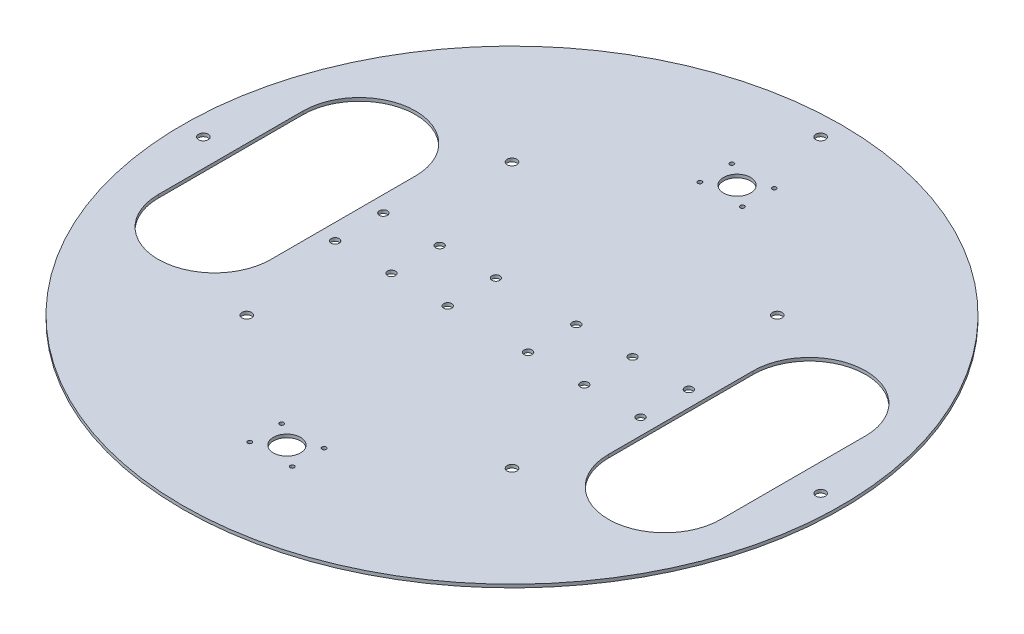
SolidWorks part; units mm, degrees
material "5052-H34"
ref_plane "Front Plane" through (0, 0, 0) normal (0, 0, 1) x (1, 0, 0)
ref_plane "Top Plane" through (0, 0, 0) normal (0, 1, 0) x (1, 0, 0)
ref_plane "Right Plane" through (0, 0, 0) normal (1, 0, 0) x (0, 0, -1)
sketch "Sketch1" plane through (0, 0, 0) normal (0, 1, 0) x (1, 0, 0)
  line L0 (0, 240.4709) -> (0, -284.4536) construction
  line L1 (-227.7898, 0) -> (257.9327, 0) construction
  line L2 (-140, 45) -> (-140, -45) construction
  line L3 (-140, 140) -> (140, 140) construction
  line L4 (-140, 140) -> (-140, -140) construction
  line L5 (-140, -140) -> (140, -140) construction
  line L6 (140, 140) -> (140, -140) construction
  line L7 (-140, 140) -> (140, -140) construction
  line L8 (-140, -140) -> (140, 140) construction
  line L9 (-105, 45) -> (-105, -45)
  line L10 (-175, 45) -> (-175, -45)
  line L11 (140, 45) -> (140, -45) construction
  line L12 (175, 45) -> (175, -45)
  line L13 (105, 45) -> (105, -45)
  line L15 (-13.2, 149.92) -> (13.2, 149.92) construction
  line L16 (-13.2, 149.92) -> (-13.2, 130.08) construction
  line L17 (-13.2, 130.08) -> (13.2, 130.08) construction
  line L18 (13.2, 149.92) -> (13.2, 130.08) construction
  line L19 (-13.2, 149.92) -> (13.2, 130.08) construction
  line L20 (-13.2, 130.08) -> (13.2, 149.92) construction
  line L22 (105, 27.5) -> (105, -27.5) construction
  line L29 (-82.5, 82.5) -> (82.5, 82.5) construction
  line L30 (-82.5, 82.5) -> (-82.5, -82.5) construction
  line L31 (-82.5, -82.5) -> (82.5, -82.5) construction
  line L32 (82.5, 82.5) -> (82.5, -82.5) construction
  line L33 (-82.5, 82.5) -> (82.5, -82.5) construction
  line L34 (-82.5, -82.5) -> (82.5, 82.5) construction
  circle A0 centre (0, 0) radius 205
  arc A1 (-105, 45) -> (-175, 45) centre (-140, 45) ccw
  arc A2 (-175, -45) -> (-105, -45) centre (-140, -45) ccw
  arc A3 (175, 45) -> (105, 45) centre (140, 45) ccw
  arc A4 (105, -45) -> (175, -45) centre (140, -45) ccw
  circle A5 centre (0, 140) radius 8.425
  circle A7 centre (0, -140) radius 8.425
  circle A8 centre (-13.2, 149.92) radius 1.31
  circle A9 centre (13.2, 149.92) radius 1.31
  circle A10 centre (13.2, 130.08) radius 1.31
  circle A11 centre (-13.2, 130.08) radius 1.31
  circle A12 centre (-13.2, -130.08) radius 1.31
  circle A13 centre (13.2, -130.08) radius 1.31
  circle A14 centre (13.2, -149.92) radius 1.31
  circle A15 centre (-13.2, -149.92) radius 1.31
  circle A24 centre (-82.5, 82.5) radius 3
  circle A25 centre (82.5, 82.5) radius 3
  circle A26 centre (82.5, -82.5) radius 3
  circle A27 centre (-82.5, -82.5) radius 3
  point P13 (-140, 0)
  point P19 (140, 0)
  dimension "D1" = 410
  dimension "D5" = 35
  dimension "D7" = 35
  dimension "D8" = 16.85
  dimension "D9" = 16.85
  dimension "D10" = 13.2
  dimension "D12" = 2.62
  dimension "D23" = 6
  dimension "D2" = 140
  dimension "D3" = 140
  dimension "D4" = 90
  dimension "D6" = 90
  dimension "D11" = 9.92
  dimension "D21" = 165
  dimension "D22" = 165
extrude "Boss-Extrude1" add sketch "Sketch1" along normal blind 2
sketch "Sketch2" plane through (0, 2, 0) normal (0, 1, 0) x (1, 0, 0)
  line L0 (0, 205) -> (0, -205) construction
  line L1 (-205, 0) -> (205, 0) construction
  circle A0 centre (0, 0) radius 205 construction
  circle A1 centre (0, 192) radius 3
  circle A2 centre (192, 0) radius 3
  circle A3 centre (-192, 0) radius 3
  dimension "D1" = 6
  dimension "D3" = 192
  dimension "D2" = 192
  dimension "D4" = 192
extrude "Cut-Extrude1" cut sketch "Sketch2" against normal through all both
sketch "Sketch3" plane through (0, 2, 0) normal (0, 1, 0) x (1, 0, 0)
  line L0 (105, 45) -> (105, -45) construction
  line L1 (95, 15) -> (25, 15) construction
  line L2 (95, 15) -> (95, -15) construction
  line L3 (95, -15) -> (25, -15) construction
  line L4 (25, 15) -> (25, -15) construction
  line L5 (0, 205) -> (0, -205) construction
  line L6 (-25, 15) -> (-25, -15) construction
  line L7 (-95, -15) -> (-25, -15) construction
  line L8 (-95, 15) -> (-95, -15) construction
  line L9 (-95, 15) -> (-25, 15) construction
  circle A0 centre (95, 15) radius 2.5
  circle A1 centre (95, -15) radius 2.5
  circle A2 centre (60, -15) radius 2.5
  circle A3 centre (25, -15) radius 2.5
  circle A4 centre (25, 15) radius 2.5
  circle A5 centre (60, 15) radius 2.5
  circle A6 centre (0, 0) radius 205 construction
  circle A7 centre (-60, 15) radius 2.5
  circle A8 centre (-25, 15) radius 2.5
  circle A9 centre (-25, -15) radius 2.5
  circle A10 centre (-60, -15) radius 2.5
  circle A11 centre (-95, -15) radius 2.5
  circle A12 centre (-95, 15) radius 2.5
  point P6 (105, 0)
  point P7 (95, 0)
  dimension "D4" = 5
  dimension "D1" = 70
  dimension "D2" = 30
  dimension "D3" = 10
extrude "Cut-Extrude2" cut sketch "Sketch3" against normal blind 10
